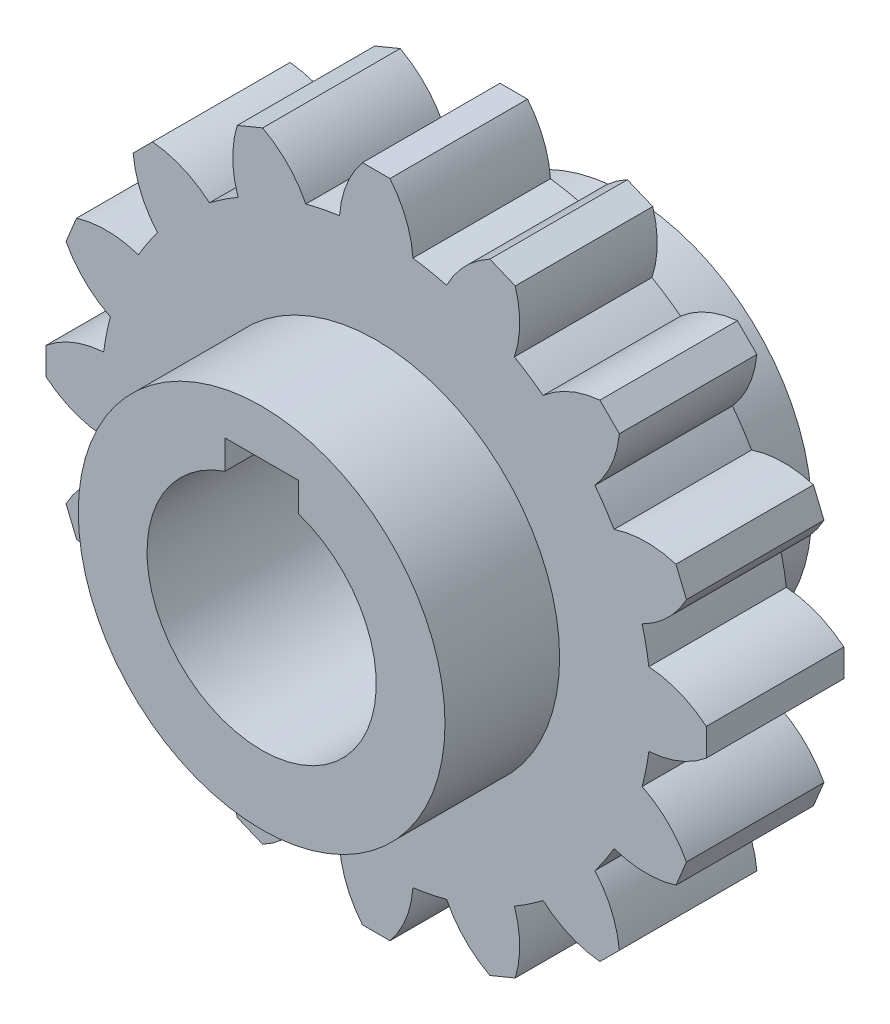
SolidWorks part; units mm, degrees
ref_plane "Front Plane" through (0, 0, 0) normal (0, 0, 1) x (1, 0, 0)
ref_plane "Top Plane" through (0, 0, 0) normal (0, 1, 0) x (1, 0, 0)
ref_plane "Right Plane" through (0, 0, 0) normal (1, 0, 0) x (0, 0, -1)
sketch "Sketch1" plane through (0, 0, 0) normal (0, 0, 1) x (1, 0, 0)
  line L0 (0, 0) -> (0, 36) construction
  line L1 (-1.5, 36) -> (1.5, 36)
  line L2 (12.3908, 33.8337) -> (15.1624, 32.6856)
  line L3 (24.3952, 26.5165) -> (26.5165, 24.3952)
  line L4 (32.6856, 15.1624) -> (33.8337, 12.3908)
  line L5 (36, 1.5) -> (36, -1.5)
  line L6 (33.8337, -12.3908) -> (32.6856, -15.1624)
  line L7 (26.5165, -24.3952) -> (24.3952, -26.5165)
  line L8 (15.1624, -32.6856) -> (12.3908, -33.8337)
  line L9 (1.5, -36) -> (-1.5, -36)
  line L10 (-12.3908, -33.8337) -> (-15.1624, -32.6856)
  line L11 (-24.3952, -26.5165) -> (-26.5165, -24.3952)
  line L12 (-32.6856, -15.1624) -> (-33.8337, -12.3908)
  line L13 (-36, -1.5) -> (-36, 1.5)
  line L14 (-33.8337, 12.3908) -> (-32.6856, 15.1624)
  line L15 (-26.5165, 24.3952) -> (-24.3952, 26.5165)
  line L16 (-15.1624, 32.6856) -> (-12.3908, 33.8337)
  arc A0 (-15.0735, 25.9382) -> (-18.1954, 23.8522) centre (0, 0) ccw
  arc A1 (-1.5, 36) -> (-4, 29.7321) centre (6.9748, 28.9873) ccw
  arc A2 (1.5, 36) -> (4, 29.7321) centre (-6.9748, 28.9873) cw
  arc A3 (12.3908, 33.8337) -> (7.6825, 28.9996) centre (17.5368, 24.1116) ccw
  arc A4 (15.1624, 32.6856) -> (15.0735, 25.9382) centre (4.6491, 29.4499) cw
  arc A5 (24.3952, 26.5165) -> (18.1954, 23.8522) centre (25.429, 15.5652) ccw
  arc A6 (26.5165, 24.3952) -> (23.8522, 18.1954) centre (15.5652, 25.429) cw
  arc A7 (32.6856, 15.1624) -> (25.9382, 15.0735) centre (29.4499, 4.6491) ccw
  arc A8 (33.8337, 12.3908) -> (28.9996, 7.6825) centre (24.1116, 17.5368) cw
  arc A9 (36, 1.5) -> (29.7321, 4) centre (28.9873, -6.9748) ccw
  arc A10 (36, -1.5) -> (29.7321, -4) centre (28.9873, 6.9748) cw
  arc A11 (33.8337, -12.3908) -> (28.9996, -7.6825) centre (24.1116, -17.5368) ccw
  arc A12 (32.6856, -15.1624) -> (25.9382, -15.0735) centre (29.4499, -4.6491) cw
  arc A13 (26.5165, -24.3952) -> (23.8522, -18.1954) centre (15.5652, -25.429) ccw
  arc A14 (24.3952, -26.5165) -> (18.1954, -23.8522) centre (25.429, -15.5652) cw
  arc A15 (15.1624, -32.6856) -> (15.0735, -25.9382) centre (4.6491, -29.4499) ccw
  arc A16 (12.3908, -33.8337) -> (7.6825, -28.9996) centre (17.5368, -24.1116) cw
  arc A17 (1.5, -36) -> (4, -29.7321) centre (-6.9748, -28.9873) ccw
  arc A18 (-1.5, -36) -> (-4, -29.7321) centre (6.9748, -28.9873) cw
  arc A19 (-12.3908, -33.8337) -> (-7.6825, -28.9996) centre (-17.5368, -24.1116) ccw
  arc A20 (-15.1624, -32.6856) -> (-15.0735, -25.9382) centre (-4.6491, -29.4499) cw
  arc A21 (-24.3952, -26.5165) -> (-18.1954, -23.8522) centre (-25.429, -15.5652) ccw
  arc A22 (-26.5165, -24.3952) -> (-23.8522, -18.1954) centre (-15.5652, -25.429) cw
  arc A23 (-32.6856, -15.1624) -> (-25.9382, -15.0735) centre (-29.4499, -4.6491) ccw
  arc A24 (-33.8337, -12.3908) -> (-28.9996, -7.6825) centre (-24.1116, -17.5368) cw
  arc A25 (-36, -1.5) -> (-29.7321, -4) centre (-28.9873, 6.9748) ccw
  arc A26 (-36, 1.5) -> (-29.7321, 4) centre (-28.9873, -6.9748) cw
  arc A27 (-33.8337, 12.3908) -> (-28.9996, 7.6825) centre (-24.1116, 17.5368) ccw
  arc A28 (-32.6856, 15.1624) -> (-25.9382, 15.0735) centre (-29.4499, 4.6491) cw
  arc A29 (-26.5165, 24.3952) -> (-23.8522, 18.1954) centre (-15.5652, 25.429) ccw
  arc A30 (-24.3952, 26.5165) -> (-18.1954, 23.8522) centre (-25.429, 15.5652) cw
  arc A31 (-15.1624, 32.6856) -> (-15.0735, 25.9382) centre (-4.6491, 29.4499) ccw
  arc A32 (-12.3908, 33.8337) -> (-7.6825, 28.9996) centre (-17.5368, 24.1116) cw
  arc A33 (-23.8522, 18.1954) -> (-25.9382, 15.0735) centre (0, 0) ccw
  arc A34 (-28.9996, 7.6825) -> (-29.7321, 4) centre (0, 0) ccw
  arc A35 (-29.7321, -4) -> (-28.9996, -7.6825) centre (0, 0) ccw
  arc A36 (-25.9382, -15.0735) -> (-23.8522, -18.1954) centre (0, 0) ccw
  arc A37 (-18.1954, -23.8522) -> (-15.0735, -25.9382) centre (0, 0) ccw
  arc A38 (-7.6825, -28.9996) -> (-4, -29.7321) centre (0, 0) ccw
  arc A39 (4, -29.7321) -> (7.6825, -28.9996) centre (0, 0) ccw
  arc A40 (15.0735, -25.9382) -> (18.1954, -23.8522) centre (0, 0) ccw
  arc A41 (23.8522, -18.1954) -> (25.9382, -15.0735) centre (0, 0) ccw
  arc A42 (28.9996, -7.6825) -> (29.7321, -4) centre (0, 0) ccw
  arc A43 (29.7321, 4) -> (28.9996, 7.6825) centre (0, 0) ccw
  arc A44 (25.9382, 15.0735) -> (23.8522, 18.1954) centre (0, 0) ccw
  arc A45 (18.1954, 23.8522) -> (15.0735, 25.9382) centre (0, 0) ccw
  arc A46 (7.6825, 28.9996) -> (4, 29.7321) centre (0, 0) ccw
  arc A47 (-4, 29.7321) -> (-7.6825, 28.9996) centre (0, 0) ccw
  point P7 (0, 36)
  point P104 (0, 0)
  dimension "D1" = 60
  dimension "D3" = 4
  dimension "D2" = 11
  dimension "D4" = 16
  dimension "D5" = 1.5
  dimension "D6" = 4
extrude "Boss-Extrude1" add sketch "Sketch1" along normal mid plane 15
sketch "Sketch2" plane through (0, 0, 0) normal (0, 0, 1) x (1, 0, 0)
  circle A0 centre (0, 0) radius 20
  dimension "D1" = 40
extrude "Boss-Extrude2" add sketch "Sketch2" along normal mid plane 40
sketch "Sketch3" plane through (0, 0, 20) normal (0, 0, 1) x (1, 0, 0)
  line L0 (0, 0) -> (0, 15) construction
  line L1 (-4, 11.8427) -> (-4, 15)
  line L2 (-4, 15) -> (4, 15)
  line L3 (4, 15) -> (4, 11.8427)
  circle A0 centre (0, 0) radius 12.5
  dimension "D1" = 25
  dimension "D2" = 15
  dimension "D3" = 8
extrude "Cut-Extrude1" cut sketch "Sketch3" against normal through all
